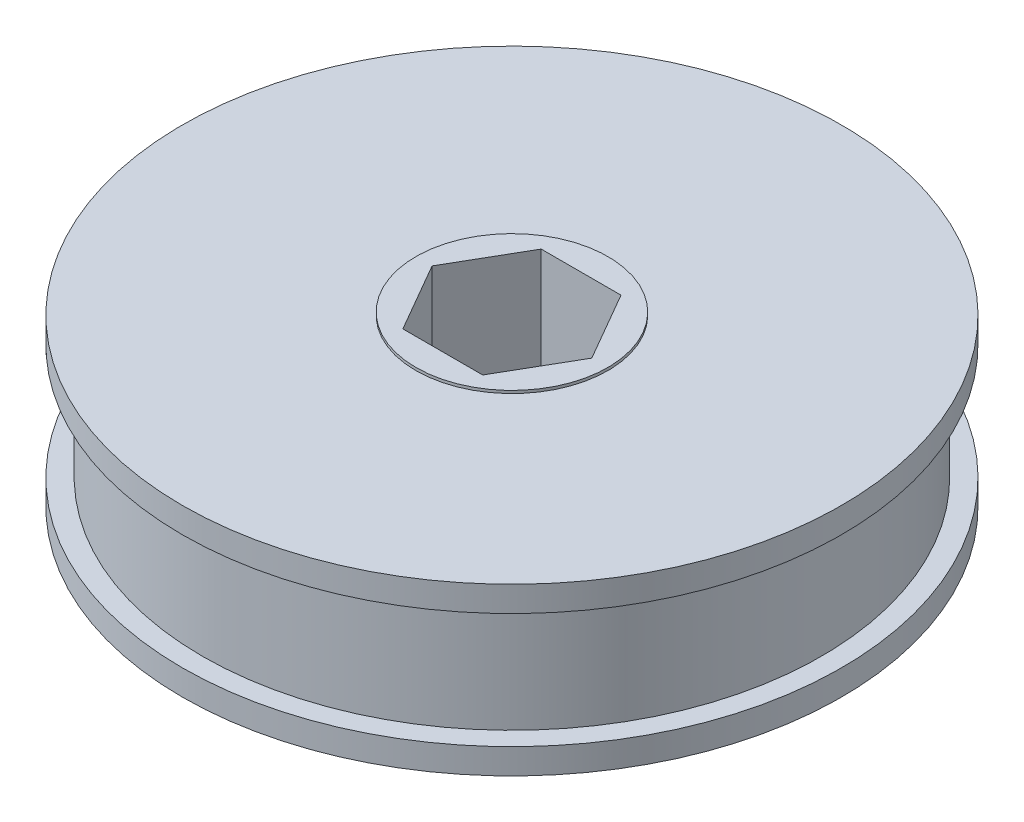
SolidWorks part; units mm, degrees
ref_plane "Front Plane" through (0, 0, 0) normal (0, 0, 1) x (1, 0, 0)
ref_plane "Top Plane" through (0, 0, 0) normal (0, 1, 0) x (1, 0, 0)
ref_plane "Right Plane" through (0, 0, 0) normal (1, 0, 0) x (0, 0, -1)
ref_axis "Axis1" through (0, 55, 0) along (0, -1, 0)
sketch "Sketch2" plane through (0, 0, 0) normal (1, 0, 0) x (0, 0, -1)
  line L0 (2.54, -3.2131) -> (8.89, -3.2131)
  line L1 (8.89, -3.2131) -> (8.89, -3.4671)
  line L2 (8.89, -3.4671) -> (30.5054, -3.4671)
  line L3 (30.5054, -3.4671) -> (30.5054, -5.8166)
  line L5 (28.6512, -5.8166) -> (28.6512, -16.4846)
  line L7 (30.5054, -16.4846) -> (30.5054, -18.8341)
  line L8 (30.5054, -18.8341) -> (8.89, -18.8341)
  line L9 (8.89, -18.8341) -> (8.89, -19.0881)
  line L10 (8.89, -19.0881) -> (2.54, -19.0881)
  line L11 (28.6512, -5.8166) -> (30.5054, -5.8166)
  line L13 (2.54, -19.0881) -> (2.54, -3.2131)
  line L14 (0, 55) -> (0, -55) construction
  line L17 (28.6512, -16.4846) -> (30.5054, -16.4846)
  dimension "D1" = 15.875
  dimension "D2" = 2.54
  dimension "D3" = 30.5054
  dimension "D4" = 6.35
  dimension "D5" = 0.254
  dimension "D6" = 10.668
  dimension "D7" = 28.6512
revolve "Revolve1" add sketch "Sketch2" angle 360 about axis through (0, 55, 0) along (0, -1, 0)
sketch "Sketch3" plane through (0, -3.2131, 0) normal (0, 1, 0) x (1, 0, 0)
  line L1 (3.6955, 6.4008) -> (-3.6955, 6.4008)
  line L2 (-3.6955, 6.4008) -> (-7.391, 0)
  line L3 (-7.391, 0) -> (-3.6955, -6.4008)
  line L4 (-3.6955, -6.4008) -> (3.6955, -6.4008)
  line L5 (3.6955, -6.4008) -> (7.391, 0)
  line L6 (7.391, 0) -> (3.6955, 6.4008)
  circle A0 centre (0, 0) radius 6.4008 construction
  dimension "D1" = 12.8016
extrude "Cut-Extrude1" cut sketch "Sketch3" against normal through all both and the other way through all
